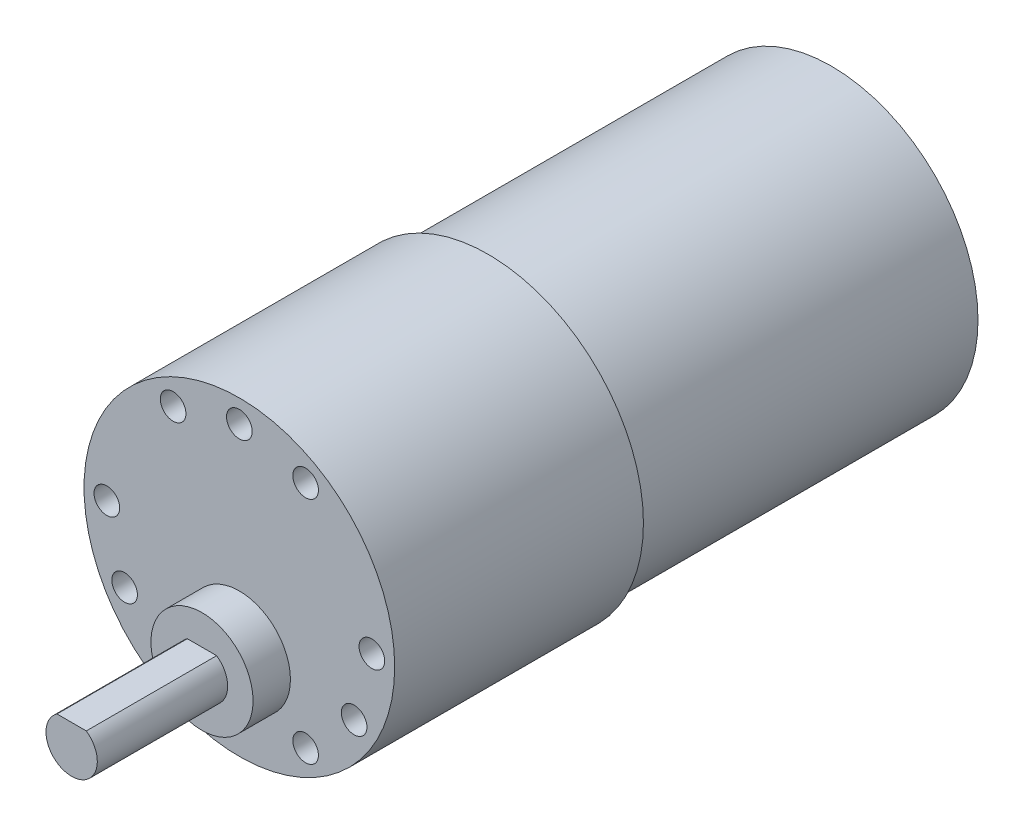
SolidWorks part; units mm, degrees
ref_plane "Front Plane" through (0, 0, 0) normal (0, 0, 1) x (1, 0, 0)
ref_plane "Top Plane" through (0, 0, 0) normal (0, 1, 0) x (1, 0, 0)
ref_plane "Right Plane" through (0, 0, 0) normal (1, 0, 0) x (0, 0, -1)
sketch "Sketch1" plane through (0, 0, 0) normal (0, 0, 1) x (1, 0, 0)
  circle A0 centre (0, 0) radius 18.161
  dimension "D1" = 36.322
extrude "Boss-Extrude1" add sketch "Sketch1" along normal blind 29.083
sketch "Sketch5" plane through (0, 0, 29.083) normal (0, 0, 1) x (1, 0, 0)
  circle A0 centre (0, -7.366) radius 5.969
  dimension "D1" = 11.938
  dimension "D2" = 7.366
extrude "Boss-Extrude5" add sketch "Sketch5" along normal blind 4.3688
sketch "Sketch6" plane through (0, 0, 33.4518) normal (0, 0, 1) x (1, 0, 0)
  line L0 (-1.7157, -4.905) -> (1.7157, -4.905)
  arc A0 (-1.7157, -4.905) -> (1.7157, -4.905) centre (0, -7.366) ccw
  dimension "D1" = 6
  dimension "D2" = 2.461
extrude "Boss-Extrude6" add sketch "Sketch6" along normal blind 15.24
sketch "Sketch9" plane through (0, 0, 29.083) normal (0, 0, 1) x (1, 0, 0)
  line L0 (0, 0) -> (0, 15.494) construction
  circle A0 centre (0, 0) radius 15.494 construction
  dimension "D1" = 30.988
hole_wizard "Ø3.0mm Dowel Hole1" positions "Sketch11" profile "Sketch12" hole size "Ø3.0" standard "ANSI Metric"
sketch "Sketch11" plane through (0, 0, 29.083) normal (0, 0, 1) x (1, 0, 0)
  point P0 (0, 15.494)
sketch "Sketch12" plane through (0, 15.494, 29.083) normal (1, 0, 0) x (0, -1, 0)
  line L0 (0, 0) -> (0, 11.0613)
  line L1 (0, 11.0613) -> (1.5, 10.16)
  line L2 (1.5, 10.16) -> (1.5, 0)
  line L5 (1.5, 0) -> (0, 0)
  line L10 (0, 11.0613) -> (-1.5, 10.16) construction
  line L11 (0, -6.35) -> (0, 107.95) construction
  dimension "Hole Dia." = 3
  dimension "Hole Depth" = 10.16
  dimension "Drill Angle" = 118
pattern_circular "CirPattern2" count 12 over 360 about axis through (0, 0, 0) along (0, 0, 1) skipping 2, 6, 10 of "Ø3.0mm Dowel Hole1"
sketch "Sketch2" plane through (0, 0, 0) normal (0, 0, -1) x (-1, 0, 0)
  circle A0 centre (0, 0) radius 17.145
  dimension "D1" = 34.29
extrude "Boss-Extrude2" add sketch "Sketch2" along normal blind 40.132
sketch "Sketch3" plane through (0, 0, -40.132) normal (0, 0, -1) x (-1, 0, 0)
  circle A0 centre (0, 0) radius 3.048
  dimension "D1" = 6.096
extrude "Boss-Extrude3" add sketch "Sketch3" along normal blind 3.81
sketch "Sketch13" plane through (0, 0, -40.132) normal (0, 0, -1) x (-1, 0, 0)
  circle A0 centre (0, 0) radius 16.637
  dimension "D1" = 33.274
extrude "Cut-Extrude1" cut sketch "Sketch13" against normal blind 1.016
sketch "Sketch14" plane through (0, 0, -39.116) normal (0, 0, -1) x (-1, 0, 0)
  line L0 (0, 0) -> (2.9583, -11.0405) construction
  line L1 (0, 0) -> (-6.5307, -7.783) construction
  circle A0 centre (0, 0) radius 11.43 construction
  circle A1 centre (0, 0) radius 10.16 construction
  dimension "D1" = 22.86
  dimension "D2" = 20.32
ref_plane "Plane1" through (0, 0, 0) normal (0.766, 0.6428, 0) x (0.6428, -0.766, 0)
ref_plane "Plane2" through (0, 0, 0) normal (0.9659, -0.2588, 0) x (-0.2588, -0.9659, 0)
sketch "Sketch15" plane through (0, 0, 0) normal (0.766, 0.6428, 0) x (0.6428, -0.766, 0)
  line L0 (8.89, 39.116) -> (8.89, 44.196)
  line L3 (10.16, 39.116) -> (-10.16, 39.116) construction
  line L4 (8.89, 44.196) -> (11.43, 44.196)
  line L5 (11.43, 44.196) -> (11.43, 39.116)
  line L6 (11.43, 39.116) -> (-11.43, 39.116) construction
  line L7 (11.43, 39.116) -> (8.89, 39.116)
  circle A0 centre (10.16, 42.926) radius 0.4445
  dimension "D4" = 0.889
  dimension "D1" = 5.08
  dimension "D2" = 2.54
  dimension "D3" = 1.27
  dimension "D5" = 1.27
  dimension "D6" = 1.27
extrude "Boss-Extrude7" add sketch "Sketch15" along normal mid plane 0.508
sketch "Sketch16" plane through (0, 0, 0) normal (0.9659, -0.2588, 0) x (-0.2588, -0.9659, 0)
  line L0 (12.7, 39.116) -> (12.7, 44.196)
  line L1 (12.7, 44.196) -> (10.16, 44.196)
  line L2 (10.16, 44.196) -> (10.16, 39.116)
  line L3 (10.16, 39.116) -> (-10.16, 39.116) construction
  line L4 (10.16, 39.116) -> (12.7, 39.116)
  circle A0 centre (11.43, 42.926) radius 0.6786
  dimension "D1" = 1.27
  dimension "D2" = 2.54
  dimension "D3" = 5.08
  dimension "D4" = 1.27
  dimension "D5" = 1.27
extrude "Boss-Extrude8" add sketch "Sketch16" along normal mid plane 0.508
